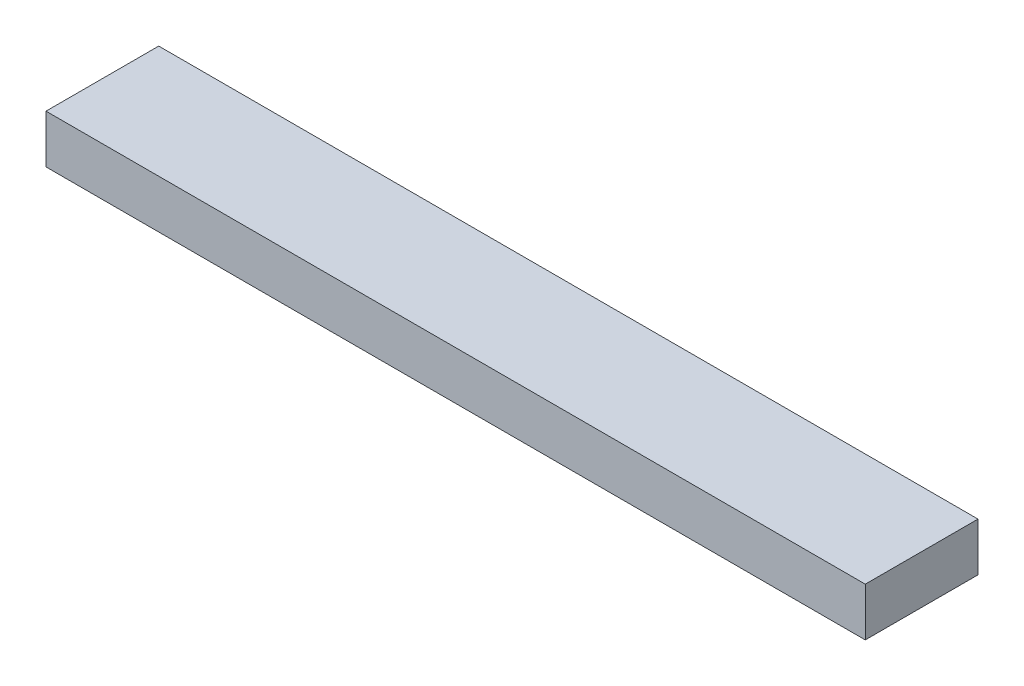
SolidWorks part; units mm, degrees
material "Pine"
ref_plane "Front Plane" through (0, 0, 0) normal (0, 0, 1) x (1, 0, 0)
ref_plane "Top Plane" through (0, 0, 0) normal (0, 1, 0) x (1, 0, 0)
ref_plane "Right Plane" through (0, 0, 0) normal (1, 0, 0) x (0, 0, -1)
sketch "Sketch1" plane through (0, 0, 0) normal (0, 1, 0) x (1, 0, 0)
  line L1 (0, 0) -> (646.1125, 0)
  line L2 (0, 0) -> (0, 88.9)
  line L3 (0, 88.9) -> (646.1125, 88.9)
  line L4 (646.1125, 0) -> (646.1125, 88.9)
  dimension "D1" = 88.9
  dimension "D2" = 646.1125
extrude "Boss-Extrude1" add sketch "Sketch1" along normal blind 38.1
